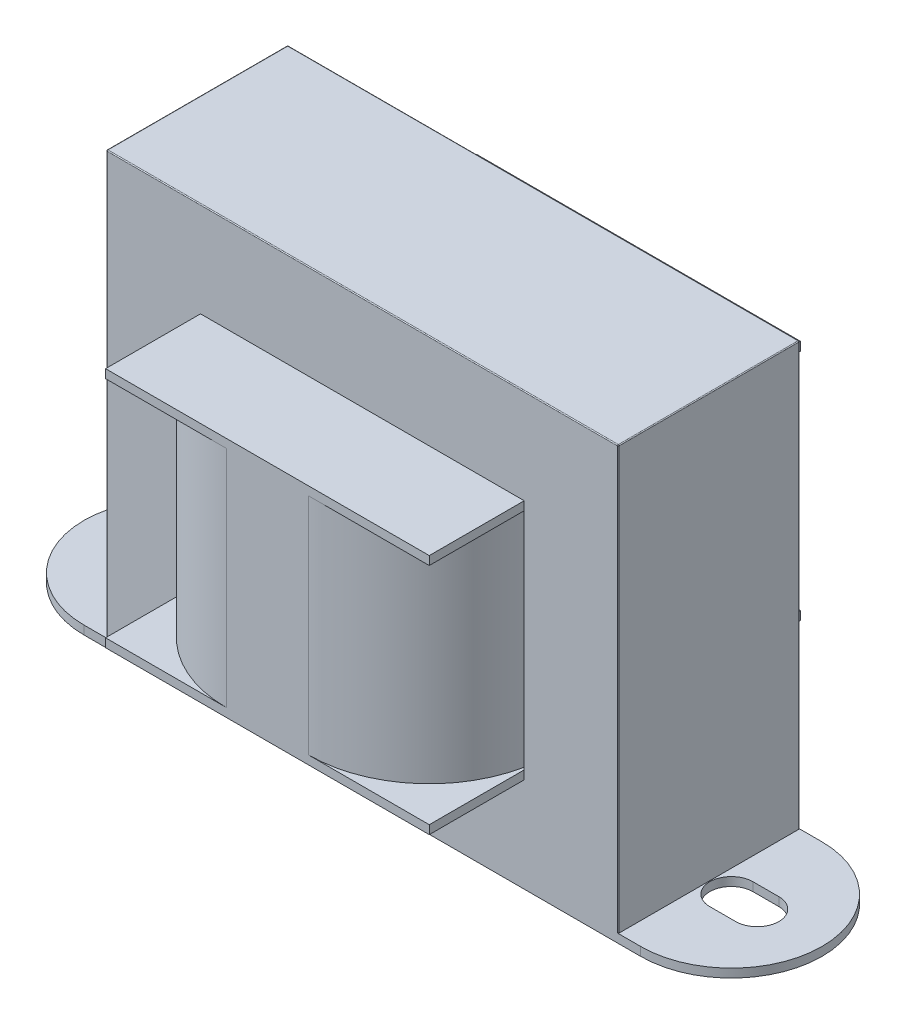
SolidWorks part; units mm, degrees
ref_plane "Front Plane" through (0, 0, 0) normal (0, 0, 1) x (1, 0, 0)
ref_plane "Top Plane" through (0, 0, 0) normal (0, 1, 0) x (1, 0, 0)
ref_plane "Right Plane" through (0, 0, 0) normal (1, 0, 0) x (0, 0, -1)
sketch "Sketch1" plane through (0, 0, 0) normal (0, 0, 1) x (1, 0, 0)
  line L1 (2.6, 49.97) -> (61.9, 49.97)
  line L2 (2.6, 49.97) -> (2.6, 1)
  line L3 (2.6, 1) -> (61.9, 1)
  line L4 (61.9, 49.97) -> (61.9, 1)
  dimension "D1" = 2.6
  dimension "D2" = 1
  dimension "D3" = 59.3
  dimension "D4" = 48.97
extrude "Base-Extrude" add sketch "Sketch1" along normal mid plane 21
sketch "Sketch2" plane through (0, 1, 0) normal (0, -1, 0) x (1, 0, 0)
  line L0 (0, 0) -> (80.8226, 0) construction
  line L1 (0, 10.5) -> (64.5, 10.5)
  line L2 (0, 0) -> (0, -18.9259) construction
  line L3 (0, -10.5) -> (64.5, -10.5)
  line L6 (64.5, 18.4078) -> (64.5, -15.4462) construction
  line L7 (0, 0) -> (0, 20.4866) construction
  arc A0 (64.5, 10.5) -> (64.5, -10.5) centre (64.5, 0) cw
  arc A1 (0, 10.5) -> (0, -10.5) centre (0, 0) ccw
  dimension "D1" = 10.5
  dimension "D4" = 10.5
  dimension "D2" = 10.5
  dimension "D3" = 64.5
extrude "Boss-Extrude1" add sketch "Sketch2" along normal blind 1
sketch "Sketch3" plane through (0, 0, 0) normal (0, -1, 0) x (1, 0, 0)
  line L0 (-3, 0) -> (77.3617, 0) construction
  line L1 (64.5, 2.5) -> (67.5, 2.5)
  line L2 (64.5, -2.5) -> (67.5, -2.5)
  line L3 (-3, 2.5) -> (0, 2.5)
  line L4 (-3, -2.5) -> (0, -2.5)
  arc A0 (-3, 2.5) -> (-3, -2.5) centre (-3, 0) ccw
  arc A1 (64.5, 2.5) -> (64.5, -2.5) centre (64.5, 0) ccw
  arc A2 (67.5, -2.5) -> (67.5, 2.5) centre (67.5, 0) ccw
  arc A3 (0, -2.5) -> (0, 2.5) centre (0, 0) ccw
  dimension "D1" = 5
  dimension "D3" = 5
  dimension "D4" = 5
  dimension "D5" = 5
  dimension "D7" = 70
  dimension "D2" = 8
  dimension "D6" = 5.5
extrude "Cut-Extrude1" cut sketch "Sketch3" against normal blind 10
ref_plane "Plane4" through (0, 24.97, 0) normal (0, 1, 0) x (-1, 0, 0)
sketch "Sketch4" plane through (0, 24.97, 0) normal (0, 1, 0) x (-1, 0, 0)
  line L0 (-32.25, -10.5) -> (-32.25, 16.7407) construction
  line L1 (-37, 21.5) -> (-27.5, 21.5)
  line L2 (-51, 7.5) -> (-51, -7.5)
  line L3 (-37, -21.5) -> (-27.5, -21.5)
  line L4 (-13.5, 7.5) -> (-13.5, -7.5)
  line L5 (-61.9, -10.5) -> (-2.6, -10.5) construction
  arc A0 (-37, -21.5) -> (-51, -7.5) centre (-37, -7.5) cw
  arc A1 (-13.5, -7.5) -> (-27.5, -21.5) centre (-27.5, -7.5) cw
  arc A2 (-13.5, 7.5) -> (-27.5, 21.5) centre (-27.5, 7.5) ccw
  arc A3 (-51, 7.5) -> (-37, 21.5) centre (-37, 7.5) cw
  point P15 (-13.5, 21.5)
  point P18 (-51, 21.5)
  dimension "D5" = 14
  dimension "D1" = 21.5
  dimension "D2" = 21.5
  dimension "D3" = 37.5
  dimension "D4" = 18.75
extrude "Boss-Extrude2" add sketch "Sketch4" along normal mid plane 26
sketch "Sketch5" plane through (0, 24.97, 0) normal (0, 1, 0) x (-1, 0, 0)
  line L0 (-13.5, 10.5) -> (-13.8252, 10.5)
  line L1 (-51, 10.5) -> (-50.6748, 10.5)
  line L2 (-51, -10.5) -> (-50.6748, -10.5)
  line L3 (-13.5, -10.5) -> (-13.8252, -10.5)
  line L4 (-51, 7.5) -> (-51, 10.5)
  line L5 (-13.5, 7.5) -> (-13.5, 10.5)
  line L6 (-13.5, -7.5) -> (-13.5, -10.5)
  line L7 (-51, -7.5) -> (-51, -10.5)
  line L8 (-61.9, 10.5) -> (-2.6, 10.5) construction
  line L9 (-61.9, -10.5) -> (-2.6, -10.5) construction
  arc A0 (-37, 21.5) -> (-51, 7.5) centre (-37, 7.5) ccw construction
  arc A1 (-51, -7.5) -> (-37, -21.5) centre (-37, -7.5) ccw construction
  arc A2 (-27.5, -21.5) -> (-13.5, -7.5) centre (-27.5, -7.5) ccw construction
  arc A3 (-13.5, 7.5) -> (-27.5, 21.5) centre (-27.5, 7.5) ccw construction
  arc A4 (-50.6748, 10.5) -> (-51, 7.5) centre (-37, 7.5) ccw
  arc A5 (-51, -7.5) -> (-50.6748, -10.5) centre (-37, -7.5) ccw
  arc A6 (-13.8252, -10.5) -> (-13.5, -7.5) centre (-27.5, -7.5) ccw
  arc A7 (-13.5, 7.5) -> (-13.8252, 10.5) centre (-27.5, 7.5) ccw
extrude "Cut-Extrude2" cut sketch "Sketch5" against normal mid plane 26
sketch "Sketch6" plane through (0, 37.97, 0) normal (0, 1, 0) x (-1, 0, 0)
  line L0 (-51, 7.5) -> (-51, -7.5) construction
  line L1 (-51, -21.5) -> (-13.5, -21.5)
  line L2 (-51, -21.5) -> (-51, 21.5)
  line L3 (-51, 21.5) -> (-13.5, 21.5)
  line L4 (-13.5, -21.5) -> (-13.5, 21.5)
  line L5 (-37, 21.5) -> (-27.5, 21.5) construction
  line L6 (-13.5, 7.5) -> (-13.5, -7.5) construction
  line L7 (-37, -21.5) -> (-27.5, -21.5) construction
extrude "Boss-Extrude3" add sketch "Sketch6" along normal blind 1
sketch "Sketch7" plane through (0, 11.97, 0) normal (0, -1, 0) x (1, 0, 0)
  line L0 (51, 7.5) -> (51, -7.5) construction
  line L1 (51, 21.5) -> (13.5, 21.5)
  line L2 (51, 21.5) -> (51, -21.5)
  line L3 (51, -21.5) -> (13.5, -21.5)
  line L4 (13.5, 21.5) -> (13.5, -21.5)
  line L5 (37, -21.5) -> (27.5, -21.5) construction
  line L6 (13.5, 7.5) -> (13.5, -7.5) construction
  line L7 (37, 21.5) -> (27.5, 21.5) construction
extrude "Boss-Extrude4" add sketch "Sketch7" along normal blind 1
fillet "Fillet1" radius 0.1 10 edges at (32.25, 49.97, 10.5) (32.25, 49.97, -10.5) (2.6, 49.97, 0) (61.9, 49.97, 0)
sketch "Component_Outline" plane through (0, 0, 0) normal (0, 1, 0) x (1, 0, 0)
  line L0 (13.5, -21.5) -> (13.5, -10.5)
  line L1 (13.5, -10.5) -> (0, -10.5)
  line L2 (0, 10.5) -> (13.5, 10.5)
  line L3 (13.5, 10.5) -> (13.5, 21.5)
  line L4 (13.5, 21.5) -> (51, 21.5)
  line L5 (51, 21.5) -> (51, 10.5)
  line L6 (51, 10.5) -> (64.5, 10.5)
  line L7 (64.5, -10.5) -> (51, -10.5)
  line L8 (51, -10.5) -> (51, -21.5)
  line L9 (51, -21.5) -> (13.5, -21.5)
  arc A0 (0, -10.5) -> (0, 10.5) centre (0, 0) cw
  arc A1 (64.5, 10.5) -> (64.5, -10.5) centre (64.5, 0) cw
